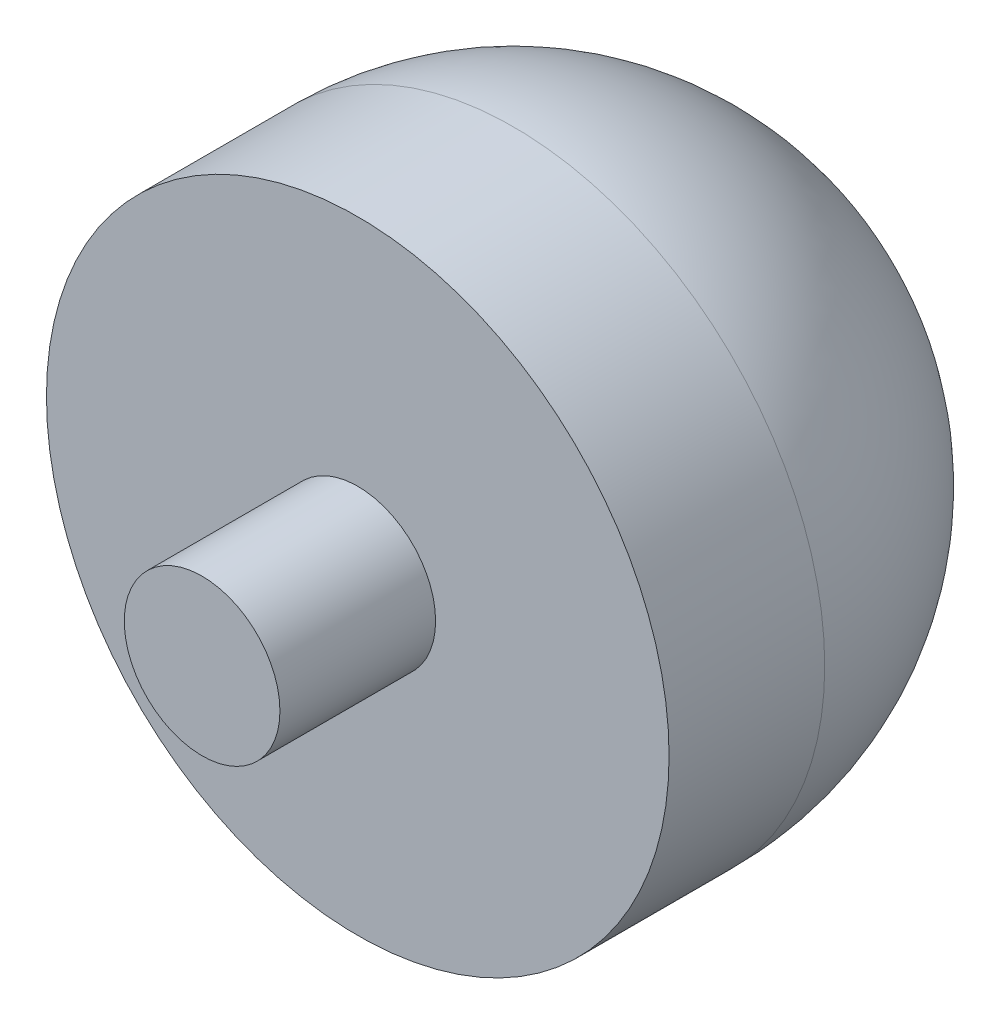
SolidWorks part; units mm, degrees
ref_plane "Front Plane" through (0, 0, 0) normal (0, 0, 1) x (1, 0, 0)
ref_plane "Top Plane" through (0, 0, 0) normal (0, 1, 0) x (1, 0, 0)
ref_plane "Right Plane" through (0, 0, 0) normal (1, 0, 0) x (0, 0, -1)
sketch "Sketch1" plane through (0, 0, 0) normal (0, 0, 1) x (1, 0, 0)
  circle A0 centre (0, 0) radius 20
  dimension "D1" = 40
extrude "Boss-Extrude1" add sketch "Sketch1" along normal blind 30
sketch "Sketch2" plane through (0, 0, 30) normal (0, 0, 1) x (1, 0, 0)
  circle A0 centre (0, 0) radius 5
  dimension "D1" = 10
extrude "Boss-Extrude2" add sketch "Sketch2" along normal blind 10
fillet "Fillet1" radius 20 1 edges at (20, 0, 0)
